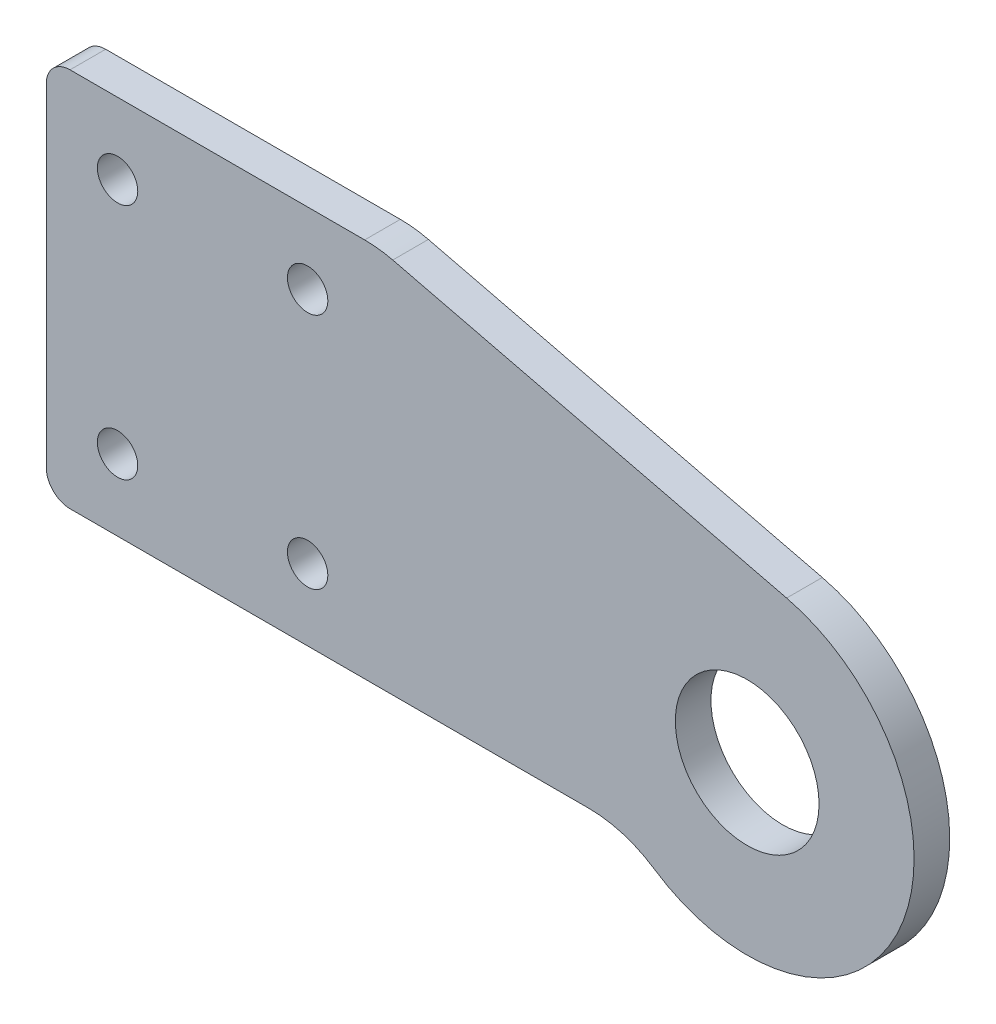
SolidWorks part; units mm, degrees
material "Hexcel AS4C (3000 Filaments)"
ref_plane "Plan de face" through (0, 0, 0) normal (0, 0, 1) x (1, 0, 0)
ref_plane "Plan de dessus" through (0, 0, 0) normal (0, 1, 0) x (1, 0, 0)
ref_plane "Plan de droite" through (0, 0, 0) normal (1, 0, 0) x (0, 0, -1)
sketch "Esquisse1" plane through (0, 0, 0) normal (0, 0, 1) x (1, 0, 0)
  line L0 (-15.5, 11) -> (1.6603, 6.826)
  line L1 (-26.5, 8) -> (-18.5, 8) construction
  line L2 (-26.5, 8) -> (-26.5, -2) construction
  line L3 (-26.5, -2) -> (-18.5, -2) construction
  line L4 (-18.5, 8) -> (-18.5, -2) construction
  line L5 (-29.5, 11) -> (-15.5, 11)
  line L6 (-29.5, 11) -> (-29.5, -5)
  line L7 (-29.5, -5) -> (-15.5, -5)
  line L8 (-15.5, 11) -> (-15.5, -5) construction
  line L9 (-15.5, -5) -> (-15.5, -1.025) construction
  line L10 (-15.5, -1.025) -> (-6.9498, -1.025) construction
  line L11 (-15.5, -5) -> (-4.9346, -5)
  circle A0 centre (0, 0) radius 3.025
  circle A1 centre (0, 0) radius 7.025 construction
  circle A2 centre (-26.5, 8) radius 0.85
  circle A3 centre (-18.5, 8) radius 0.85
  circle A4 centre (-18.5, -2) radius 0.85
  circle A5 centre (-26.5, -2) radius 0.85
  arc A6 (-6.9498, -1.025) -> (1.6603, 6.826) centre (0, 0) ccw construction
  arc A7 (-4.9346, -5) -> (1.6603, 6.826) centre (0, 0) ccw
  dimension "D1" = 8
  dimension "D8" = 14.05
  dimension "D9" = 6.05
  dimension "D10" = 1.7
  dimension "D11" = 1.7
  dimension "D12" = 1.7
  dimension "D13" = 1.7
  dimension "D2" = 10
  dimension "D3" = 3
  dimension "D4" = 14
  dimension "D5" = 3
  dimension "D6" = 16
  dimension "D7" = 5
  dimension "D14" = 3.975
  dimension "D15" = 29.5
extrude "Boss.-Extru.1" add sketch "Esquisse1" along normal mid plane 1.5
fillet "Congé1" radius 5 2 edges at (-15.5, 11, 0) (-4.9346, -5, 0)
fillet "Congé2" radius 1 2 edges at (-29.5, -5, 0) (-29.5, 11, 0)
